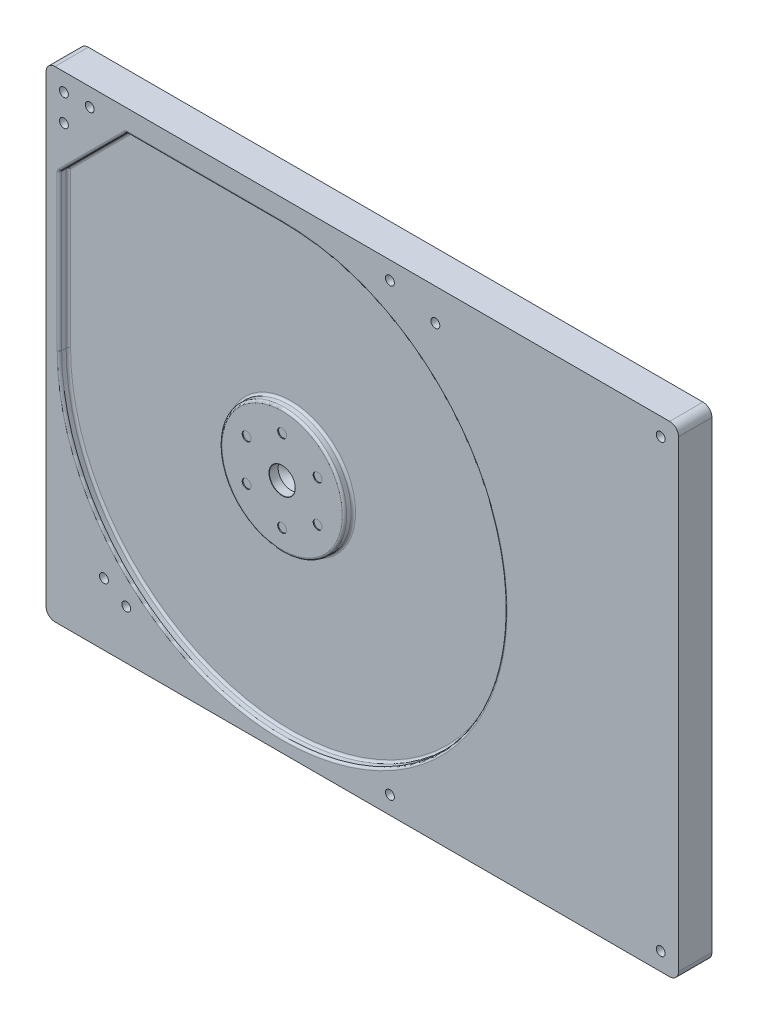
SolidWorks part; units mm, degrees
material "6061-T6 (SS)"
ref_plane "Front Plane" through (0, 0, 0) normal (0, 0, 1) x (1, 0, 0)
ref_plane "Top Plane" through (0, 0, 0) normal (0, 1, 0) x (1, 0, 0)
ref_plane "Right Plane" through (0, 0, 0) normal (1, 0, 0) x (0, 0, -1)
sketch "Sketch1" plane through (0, 0, 0) normal (0, 0, 1) x (1, 0, 0)
  line L1 (-35.5, -27) -> (35.5, -27)
  line L2 (-35.5, -27) -> (-35.5, 27)
  line L3 (-35.5, 27) -> (35.5, 27)
  line L4 (35.5, -27) -> (35.5, 27)
  line L5 (-35.5, -27) -> (35.5, 27) construction
  line L6 (-35.5, 27) -> (35.5, -27) construction
  point P0 (0, 0)
  dimension "D1" = 71
  dimension "D2" = 54
extrude "Boss-Extrude1" add sketch "Sketch1" along normal blind 3.75
fillet "Fillet1" radius 1 4 edges at (-35.5, -27, 1.875) (35.5, -27, 1.875) (35.5, 27, 1.875) (-35.5, 27, 1.875)
sketch "Sketch2" plane through (0, 0, 3.75) normal (0, 0, 1) x (1, 0, 0)
  line L0 (-35.5, 26) -> (-35.5, -26) construction
  line L1 (-34.5, -27) -> (34.5, -27) construction
  line L2 (-34, -0.5) -> (-34, 17)
  line L3 (-9, 24.5) -> (-26.5, 24.5)
  line L4 (-34, 17) -> (-26.5, 24.5)
  circle A0 centre (-9, -0.5) radius 7
  arc A1 (-34, -0.5) -> (-9, 24.5) centre (-9, -0.5) ccw
  point P0 (-9, -0.5)
  dimension "D3" = 50
  dimension "D4" = 14
  dimension "D1" = 26.5
  dimension "D2" = 26.5
  dimension "D5" = 9
extrude "Cut-Extrude1" cut sketch "Sketch2" against normal blind 1
fillet "Fillet2" radius 0.25 1 edges at (-2, -0.5, 3.75)
sketch "Sketch3" plane through (0, 0, 3.75) normal (0, 0, 1) x (1, 0, 0)
  circle A0 centre (-9, -0.5) radius 4.6 construction
  circle A1 centre (-9, 4.1) radius 0.5
  circle A2 centre (-12.9837, 1.8) radius 0.5
  circle A3 centre (-12.9837, -2.8) radius 0.5
  circle A4 centre (-9, -5.1) radius 0.5
  circle A5 centre (-5.0163, -2.8) radius 0.5
  circle A6 centre (-5.0163, 1.8) radius 0.5
  point P17 (-9, -0.5)
  dimension "D1" = 9.2
  dimension "D2" = 1
  dimension "D3" = 6
extrude "Cut-Extrude2" cut sketch "Sketch3" against normal blind 0.1
fillet "Fillet3" radius 0.25 11 edges at (8.6777, -18.1777, 3.75) (-34, 8.25, 3.75) (-34, 17, 3.25) (-30.25, 20.75, 3.75) (-26.5, 24.5, 3.25) (-17.75, 24.5, 3.75) (-34, 8.25, 2.75) (-30.25, 20.75, 2.75) (-17.75, 24.5, 2.75) (8.6777, -18.1777, 2.75) (-2, -0.5, 2.75)
hole_wizard "M2.5 Clearance Hole1" positions "Sketch5" profile "Sketch6" hole size "M2.5" standard "ANSI Metric"
sketch "Sketch5" plane through (0, 0, 3.75) normal (0, 0, 1) x (1, 0, 0)
  point P0 (-9, -0.5)
sketch "Sketch6" plane through (-9, -0.5, 3.75) normal (1, 0, 0) x (0, -1, 0)
  line L0 (0, 0) -> (0, 1.8712)
  line L1 (0, 1.8712) -> (1.45, 1)
  line L2 (1.45, 1) -> (1.45, 0.025)
  line L3 (1.45, 0.025) -> (1.475, 0)
  line L5 (1.475, 0) -> (0, 0)
  line L6 (-1.45, 0.025) -> (-1.475, 0) construction
  line L10 (0, 1.8712) -> (-1.45, 1) construction
  line L11 (0, -6.35) -> (0, 107.95) construction
  dimension "Hole Dia." = 2.9
  dimension "Hole Depth" = 1
  dimension "Near C'Sink Dia." = 2.95
  dimension "Near C'Sink Angle" = 90
  dimension "Drill Angle" = 118
sketch "Sketch7" plane through (0, 0, 3.75) normal (0, 0, 1) x (1, 0, 0)
  line L0 (-35.5, 26) -> (-35.5, -26) construction
  line L1 (34.5, 27) -> (-34.5, 27) construction
  line L2 (33.5, 27) -> (33.5, -27) construction
  line L3 (-33.5, 25) -> (-33.5, 22) construction
  line L4 (-35.5, 25) -> (35.5, 25) construction
  line L5 (35.5, -26) -> (35.5, 26) construction
  line L6 (-34.5, -27) -> (34.5, -27) construction
  line L7 (35.5, -25) -> (-35.5, -25) construction
  line L8 (3.1, 25) -> (3.1, -25) construction
  point P0 (-33.5, 25)
  point P1 (-30.6, 25)
  point P6 (3.1, 25)
  point P10 (-33.5, 22)
  point P11 (8.2, 23.4)
  point P19 (33.5, -25)
  point P22 (3.1, -25)
  point P23 (33.5, 25)
  point P26 (-29, -20)
  point P27 (-26.5, -21.5)
  dimension "D1" = 2
  dimension "D2" = 4.9
  dimension "D3" = 2
  dimension "D4" = 5
  dimension "D5" = 2
  dimension "D6" = 38.6
  dimension "D7" = 3.6
  dimension "D8" = 43.7
  dimension "D9" = 2
  dimension "D10" = 2
  dimension "D11" = 6.5
  dimension "D12" = 9
  dimension "D13" = 7
  dimension "D14" = 5.5
hole_wizard "M1.6 Clearance Hole1" positions "Sketch8" profile "Sketch9" hole size "M1.6" standard "ANSI Metric" end condition through all
sketch "Sketch8" plane through (0, 0, 3.75) normal (0, 0, 1) x (1, 0, 0)
  point P0 (-169.7807, 67.4579)
  point P2 (-33.5, 22)
  point P5 (-30.6, 25)
  point P8 (3.1, 25)
  point P11 (33.5, 25)
  point P14 (8.2, 23.4)
  point P17 (33.5, -25)
  point P20 (3.1, -25)
  point P23 (-26.5, -21.5)
  point P26 (-29, -20)
  point P29 (-33.5, 25)
sketch "Sketch9" plane through (-169.7807, 67.4579, 3.75) normal (1, 0, 0) x (0, -1, 0)
  line L0 (0, 0) -> (0, 3.75)
  line L1 (0, 3.75) -> (0.5, 3.75)
  line L2 (0.5, 3.75) -> (0.5, 0)
  line L5 (0.5, 0) -> (0, 0)
  line L11 (0, -6.35) -> (0, 107.95) construction
  dimension "Thru Hole Dia." = 1
  dimension "Thru Hole Depth" = 3.75
sketch "HDD Mounting Screw Pattern" plane through (0, 0, 3.75) normal (0, 0, 1) x (1, 0, 0)
  point P0 (-33.5, 25)
  point P1 (3.1, 25)
  point P3 (8.2, 23.4)
  point P5 (33.5, 25)
  point P7 (33.5, -25)
  point P9 (3.1, -25)
